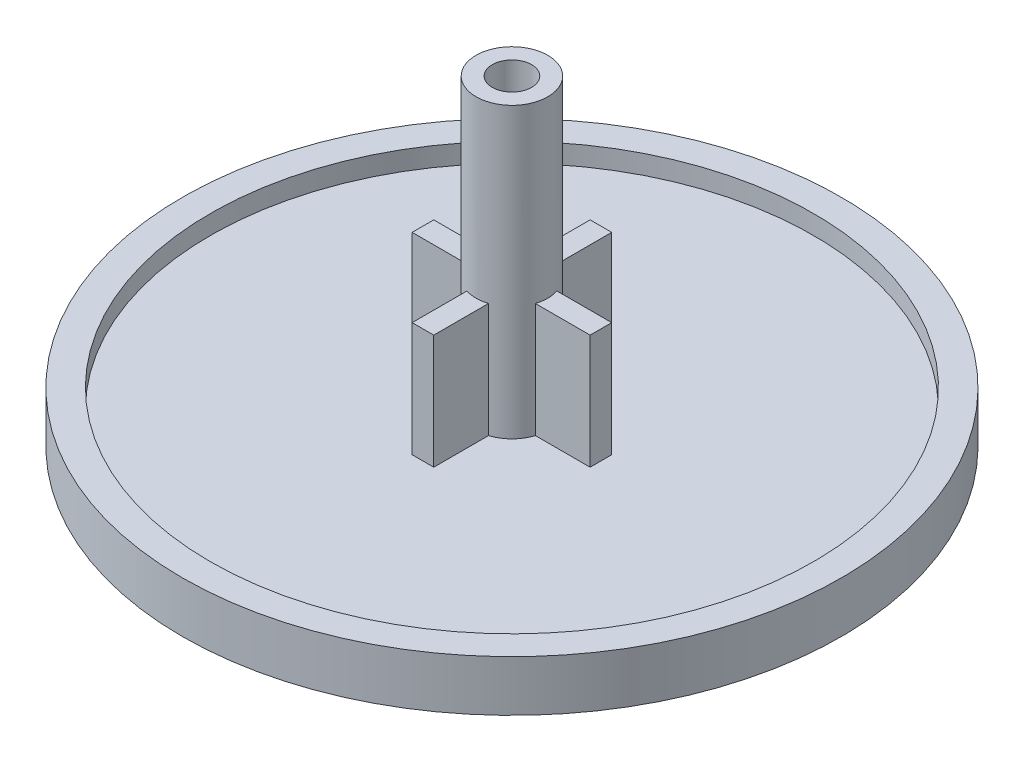
SolidWorks part; units mm, degrees
material "ABS"
ref_plane "Front Plane" through (0, 0, 0) normal (0, 0, 1) x (1, 0, 0)
ref_plane "Top Plane" through (0, 0, 0) normal (0, 1, 0) x (1, 0, 0)
ref_plane "Right Plane" through (0, 0, 0) normal (1, 0, 0) x (0, 0, -1)
sketch "Sketch1" plane through (0, 0, 0) normal (0, 1, 0) x (1, 0, 0)
  circle A0 centre (0, 0) radius 13.1699
  dimension "D1" = 26.3398
extrude "Boss-Extrude1" add sketch "Sketch1" along normal blind 1.27
sketch "Sketch2" plane through (0, 1.27, 0) normal (0, 1, 0) x (1, 0, 0)
  circle A0 centre (0, 0) radius 12.0523
  circle A1 centre (0, 0) radius 13.1699 construction
  circle A3 centre (0, 0) radius 13.1699
  circle A4 centre (0, 0) radius 13.1699
  dimension "D1" = 1.1176
  dimension "D2" = 0
extrude "Boss-Extrude2" add sketch "Sketch2" along normal blind 0.762
sketch "Sketch3" plane through (0, 1.27, 0) normal (0, 1, 0) x (1, 0, 0)
  circle A0 centre (0, 0) radius 1.4351
  dimension "D1" = 2.8702
extrude "Boss-Extrude3" add sketch "Sketch3" along normal blind 11.5443
sketch "Sketch6" plane through (0, 0, 0) normal (0, 0, 1) x (1, 0, 0)
  line L0 (13.1699, 2.032) -> (-13.1699, 2.032) construction
  line L1 (-3.556, 0) -> (3.556, 0)
  line L2 (-3.556, 0) -> (-3.556, 5.842)
  line L3 (-3.556, 5.842) -> (3.556, 5.842)
  line L4 (3.556, 0) -> (3.556, 5.842)
  line L5 (-3.556, 0) -> (3.556, 5.842) construction
  line L6 (-3.556, 5.842) -> (3.556, 0) construction
  line L7 (-13.1699, 0) -> (13.1699, 0) construction
  point P4 (0, 2.921)
  dimension "D1" = 7.112
  dimension "D2" = 3.81
extrude "Boss-Extrude4" add sketch "Sketch6" along normal mid plane 0.8636
sketch "Sketch7" plane through (0, 0, 0) normal (1, 0, 0) x (0, 0, -1)
  line L0 (-13.1699, 0) -> (13.1699, 0) construction
  line L1 (-3.556, 0) -> (3.556, 0)
  line L2 (-3.556, 0) -> (-3.556, 5.842)
  line L3 (-3.556, 5.842) -> (3.556, 5.842)
  line L4 (3.556, 0) -> (3.556, 5.842)
  line L5 (-3.556, 0) -> (3.556, 5.842) construction
  line L6 (-3.556, 5.842) -> (3.556, 0) construction
  line L7 (-0.4318, 5.842) -> (0.4318, 5.842) construction
  point P4 (0, 2.921)
  dimension "D1" = 7.112
extrude "Boss-Extrude5" add sketch "Sketch7" along normal mid plane 0.8636
sketch "Sketch4" plane through (0, 12.8143, 0) normal (0, 1, 0) x (1, 0, 0)
  circle A0 centre (0, 0) radius 0.7874
  dimension "D1" = 1.5748
extrude "Cut-Extrude1" cut sketch "Sketch4" against normal up to surface (11.5443 mm away) up to face at (0, 1.27, 12.0523)
